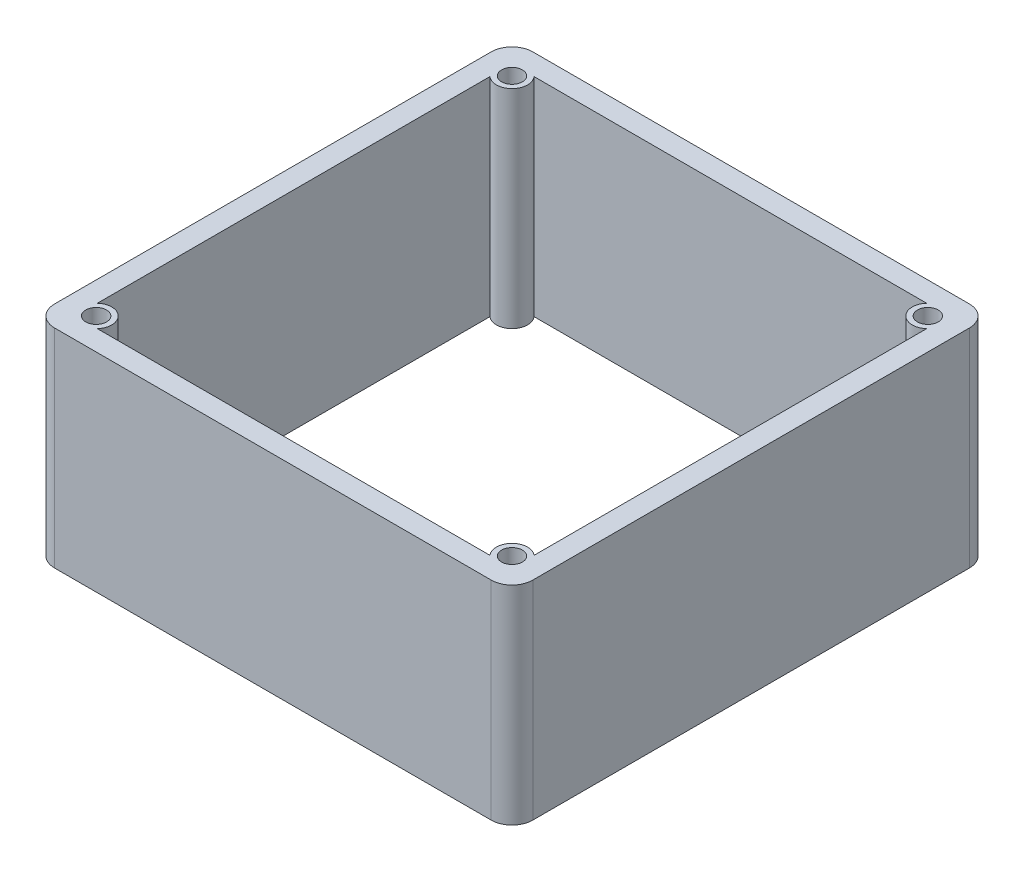
SolidWorks part; units mm, degrees
ref_plane "Front Plane" through (0, 0, 0) normal (0, 0, 1) x (1, 0, 0)
ref_plane "Top Plane" through (0, 0, 0) normal (0, 1, 0) x (1, 0, 0)
ref_plane "Right Plane" through (0, 0, 0) normal (1, 0, 0) x (0, 0, -1)
sketch "Sketch1" plane through (0, 0, 0) normal (0, 1, 0) x (1, 0, 0)
  line L1 (-23, 23) -> (23, 23)
  line L2 (-23, 23) -> (-23, -23)
  line L3 (-23, -23) -> (23, -23)
  line L4 (23, 23) -> (23, -23)
  line L5 (-23, 23) -> (23, -23) construction
  line L6 (-23, -23) -> (23, 23) construction
  line L7 (-18.882, 21) -> (18.882, 21)
  line L8 (-21, 18.882) -> (-21, -18.882)
  line L9 (-18.882, -21) -> (18.882, -21)
  line L10 (21, 18.882) -> (21, -18.882)
  line L11 (-21, 21) -> (21, -21) construction
  line L12 (-21, -21) -> (21, 21) construction
  arc A0 (-18.882, -21) -> (-21, -18.882) centre (-20, -20) ccw
  arc A1 (21, -18.882) -> (18.882, -21) centre (20, -20) ccw
  circle A2 centre (-20, 20) radius 1
  arc A3 (-21, 18.882) -> (-18.882, 21) centre (-20, 20) ccw
  arc A4 (18.882, 21) -> (21, 18.882) centre (20, 20) ccw
  circle A5 centre (20, 20) radius 1
  circle A6 centre (20, -20) radius 1
  circle A7 centre (-20, -20) radius 1
  point P0 (0, 0)
  point P6 (0, 0)
  dimension "D4" = 2
  dimension "D6" = 3
  dimension "D7" = 3
  dimension "D8" = 3
  dimension "D9" = 3
  dimension "D10" = 3
  dimension "D11" = 3
  dimension "D12" = 3
  dimension "D1" = 46
  dimension "D2" = 46
  dimension "D3" = 2
  dimension "D5" = 2
extrude "Boss-Extrude1" add sketch "Sketch1" along normal blind 20
fillet "Fillet1" radius 2 4 edges at (-23, 10, 23) (23, 10, 23) (23, 10, -23) (-23, 10, -23)
